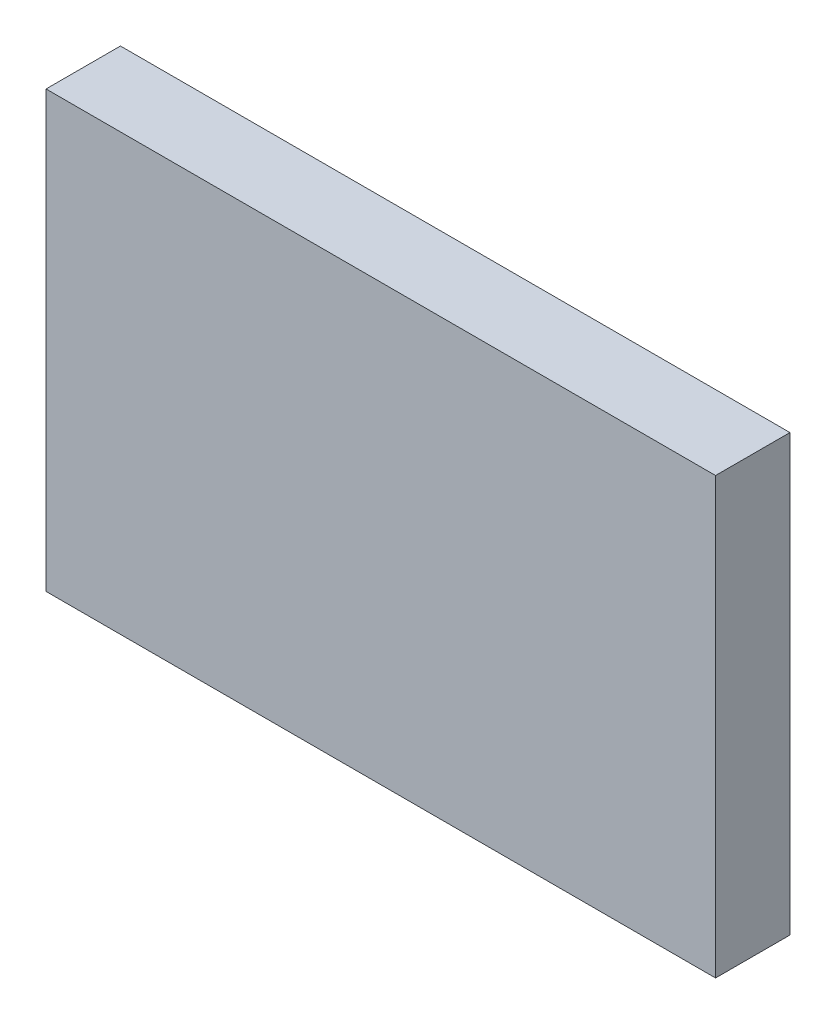
SolidWorks part; units mm, degrees
ref_plane "Front Plane" through (0, 0, 0) normal (0, 0, 1) x (1, 0, 0)
ref_plane "Top Plane" through (0, 0, 0) normal (0, 1, 0) x (1, 0, 0)
ref_plane "Right Plane" through (0, 0, 0) normal (1, 0, 0) x (0, 0, -1)
sketch "Sketch1" plane through (0, 0, 0) normal (0, 0, 1) x (1, 0, 0)
  line L5 (-22.86, -14.859) -> (22.86, -14.859)
  line L6 (-22.86, -14.859) -> (-22.86, 14.859)
  line L7 (-22.86, 14.859) -> (22.86, 14.859)
  line L8 (22.86, -14.859) -> (22.86, 14.859)
  line L9 (-22.86, -14.859) -> (22.86, 14.859) construction
  line L10 (-22.86, 14.859) -> (22.86, -14.859) construction
  point P0 (0, 0)
  dimension "D1" = 45.72
  dimension "D2" = 29.718
extrude "Boss-Extrude1" add sketch "Sketch1" along normal blind 5.08
